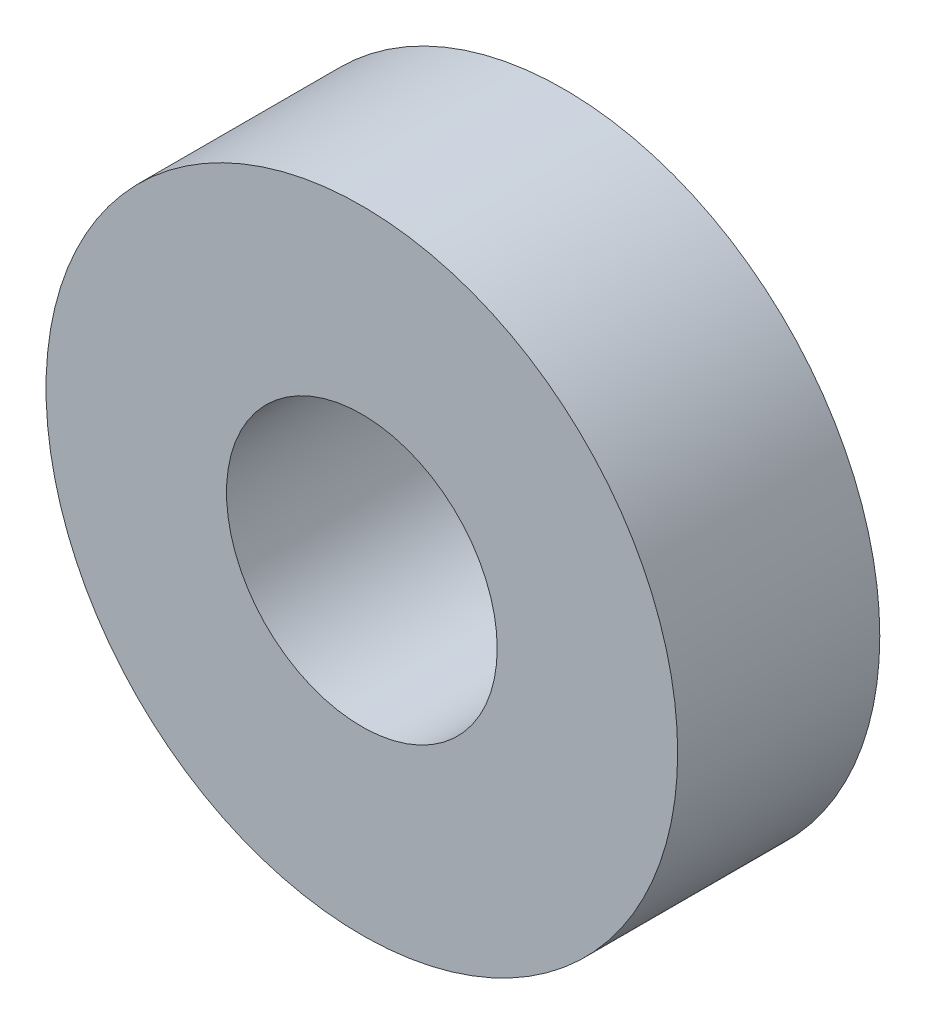
SolidWorks part; units mm, degrees
ref_plane "Front Plane" through (0, 0, 0) normal (0, 0, 1) x (1, 0, 0)
ref_plane "Top Plane" through (0, 0, 0) normal (0, 1, 0) x (1, 0, 0)
ref_plane "Right Plane" through (0, 0, 0) normal (1, 0, 0) x (0, 0, -1)
sketch "Sketch1" plane through (0, 0, 0) normal (0, 0, 1) x (1, 0, 0)
  circle A0 centre (0, 0) radius 11.1125
  circle A1 centre (0, 0) radius 4.7625
  dimension "D1" = 22.225
  dimension "D2" = 9.525
extrude "Boss-Extrude1" add sketch "Sketch1" along normal blind 7.112
